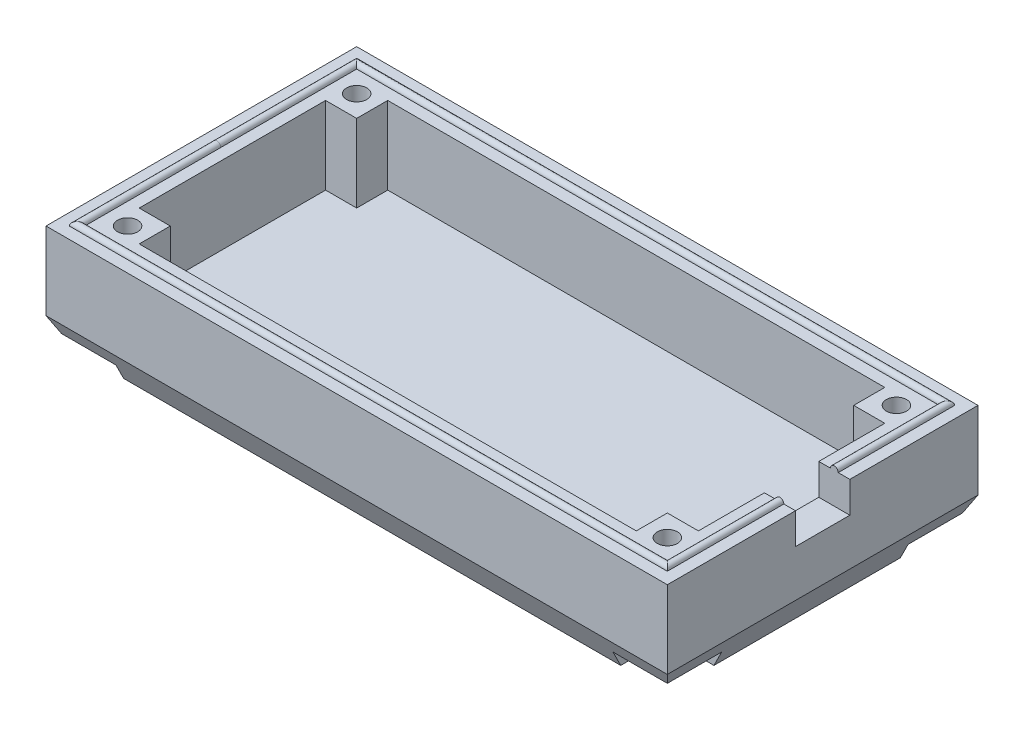
SolidWorks part; units mm, degrees
ref_plane "Piano frontale" through (0, 0, 0) normal (0, 0, 1) x (1, 0, 0)
ref_plane "Piano superiore" through (0, 0, 0) normal (0, 1, 0) x (1, 0, 0)
ref_plane "Piano destro" through (0, 0, 0) normal (1, 0, 0) x (0, 0, -1)
sketch "Schizzo2" plane through (0, 0, 0) normal (0, 1, 0) x (1, 0, 0)
  line L1 (20, -10) -> (-20, -10)
  line L2 (20, -10) -> (20, 10)
  line L3 (20, 10) -> (-20, 10)
  line L4 (-20, -10) -> (-20, 10)
  line L5 (20, -10) -> (-20, 10) construction
  line L6 (20, 10) -> (-20, -10) construction
  point P0 (0, 0)
  dimension "D1" = 40
  dimension "D2" = 20
extrude "Estrusione-Estrusione1" add sketch "Schizzo2" against normal blind 7
sketch "Schizzo3" plane through (0, 0, 0) normal (0, 1, 0) x (1, 0, 0)
  line L0 (20, 10) -> (-20, 10) construction
  line L1 (-16, 8) -> (16, 8)
  line L2 (-18, 6) -> (-18, -6)
  line L3 (-16, -8) -> (16, -8)
  line L4 (18, 6) -> (18, -6)
  line L5 (-16, 7.1111) -> (16, -7.1111) construction
  line L6 (-16, -7.1111) -> (16, 7.1111) construction
  line L7 (-18, 6) -> (-16, 6)
  line L8 (-20, 10) -> (-20, -10) construction
  line L9 (-16, 6) -> (-16, 8)
  line L10 (16, -8) -> (16, -6)
  line L11 (16, -6) -> (18, -6)
  line L12 (18, 6) -> (16, 6)
  line L13 (16, 6) -> (16, 8)
  line L14 (-16, -8) -> (-16, -6)
  line L15 (-16, -6) -> (-18, -6)
  point P0 (0, 0)
  dimension "D1" = 2
  dimension "D2" = 2
  dimension "D3" = 2
extrude "Taglio-Estrusione1" cut sketch "Schizzo3" against normal blind 5
sketch "Schizzo4" plane through (0, 0, 0) normal (0, 0, 1) x (1, 0, 0)
  line L0 (-20, 0) -> (20, 0) construction
  line L1 (-18.75, 0) -> (-19.25, 0)
  arc A0 (-18.75, 0) -> (-19.25, 0) centre (-19, 0) ccw
  dimension "D2" = 0.5
  dimension "D1" = 1
sketch "Schizzo5" plane through (0, 0, 0) normal (0, 1, 0) x (1, 0, 0)
  line L0 (-20, 10) -> (-20, -10) construction
  line L1 (19, -9) -> (-19, -9)
  line L2 (19, -9) -> (19, 9)
  line L3 (19, 9) -> (-19, 9)
  line L4 (-19, -9) -> (-19, 9)
  line L5 (19, -9) -> (-19, 9) construction
  line L6 (19, 9) -> (-19, -9) construction
  line L7 (20, 10) -> (-20, 10) construction
  point P0 (0, 0)
  dimension "D1" = 1
  dimension "D2" = 1
sweep "Sweep1" add profiles "Schizzo4" path "Schizzo5"
chamfer "Smusso1" distance 1 distance2 2 4 edges at (0, -7, 10) (20, -7, 0) (0, -7, -10) (-20, -7, 0)
sketch "Schizzo6" plane through (0, -7, 0) normal (0, -1, 0) x (1, 0, 0)
  line L1 (-20, 10) -> (-16, 10)
  line L2 (-20, 10) -> (-20, 6)
  line L3 (-20, 6) -> (-16, 6)
  line L4 (-16, 10) -> (-16, 6)
  line L5 (20, 10) -> (16, 10)
  line L6 (20, 10) -> (20, 6)
  line L7 (20, 6) -> (16, 6)
  line L8 (16, 10) -> (16, 6)
  line L9 (20, -10) -> (16, -10)
  line L10 (20, -10) -> (20, -6)
  line L11 (20, -6) -> (16, -6)
  line L12 (16, -10) -> (16, -6)
  line L13 (-20, -10) -> (-16, -10)
  line L14 (-20, -10) -> (-20, -6)
  line L15 (-20, -6) -> (-16, -6)
  line L16 (-16, -10) -> (-16, -6)
  dimension "D1" = 4
extrude "Taglio-Estrusione2" cut sketch "Schizzo6" against normal blind 1
hole_wizard "Foro per Vite M1-1" positions "Schizzo12" profile "Schizzo13" hole size "M1" standard "ISO" end condition through all
sketch "Schizzo12" plane through (0, -6, 0) normal (0, -1, 0) x (-1, 0, 0)
  line L0 (-20, -10) -> (-20, 10) construction
  line L2 (-20, 10) -> (20, 10) construction
  point P0 (-17.375, 7.375)
  dimension "D1" = 2.625
  dimension "D2" = 2.625
sketch "Schizzo13" plane through (17.375, -6, -7.375) normal (1, 0, 0) x (0, 0, -1)
  line L0 (0, 0) -> (0, 6.25)
  line L1 (0, 6.25) -> (0.65, 6.25)
  line L2 (0.65, 6.25) -> (0.65, 0.025)
  line L3 (0.65, 0.025) -> (0.675, 0)
  line L5 (0.675, 0) -> (0, 0)
  line L6 (-0.65, 0.025) -> (-0.675, 0) construction
  line L11 (0, -6.35) -> (0, 107.95) construction
  dimension "Thru Hole Dia." = 1.3
  dimension "Thru Hole Depth" = 6.25
  dimension "Near C'Sink Dia." = 1.35
  dimension "Near C'Sink Angle" = 90
cosmetic thread "Cosmetic Thread1" parameters "D2"=2.3
mirror "Specchia1" about plane through (0, 0, 0) normal (1, 0, 0) of "Foro per Vite M1-1"
cosmetic thread "Cosmetic Thread2" parameters "D2"=2.3
mirror "Specchia2" about plane through (0, 0, 0) normal (0, 0, 1) of "Specchia1", "Foro per Vite M1-1"
cosmetic thread "Cosmetic Thread3" parameters "D2"=2.3
cosmetic thread "Cosmetic Thread4" parameters "D2"=2.3
sketch "Schizzo14" plane through (20, 0, 0) normal (1, 0, 0) x (0, 0, -1)
  line L1 (-1.75, 2) -> (1.75, 2)
  line L2 (-1.75, 2) -> (-1.75, -2)
  line L3 (-1.75, -2) -> (1.75, -2)
  line L4 (1.75, 2) -> (1.75, -2)
  line L5 (-1.75, 2) -> (1.75, -2) construction
  line L6 (-1.75, -2) -> (1.75, 2) construction
  point P0 (0, 0)
  dimension "D1" = 2
  dimension "D2" = 3.5
extrude "Taglio-Estrusione3" cut sketch "Schizzo14" against normal blind 3 and the other way through all
